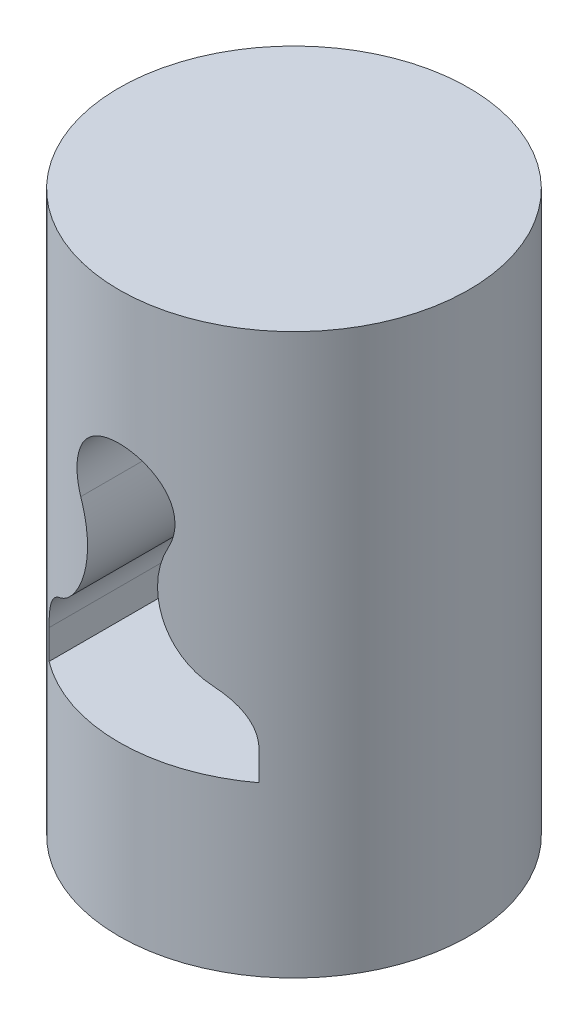
SolidWorks part; units mm, degrees
ref_plane "Front" through (0, 0, 0) normal (0, 0, 1) x (1, 0, 0)
ref_plane "Top" through (0, 0, 0) normal (0, 1, 0) x (1, 0, 0)
ref_plane "Right" through (0, 0, 0) normal (1, 0, 0) x (0, 0, -1)
sketch "Sketch2" plane through (0, 0, 0) normal (0, 1, 0) x (1, 0, 0)
  circle A0 centre (0, 0) radius 12.5
  dimension "D1" = 25
extrude "Boss-Extrude1" add sketch "Sketch2" along normal mid plane 40
sketch "Sketch3" plane through (0, 0, 0) normal (0, 0, 1) x (1, 0, 0)
  line L0 (-7.5, -8) -> (7.5, -8)
  line L1 (7.5, -8) -> (7.5, -5.9029)
  line L2 (-7.5, -5.9029) -> (-7.5, -8)
  arc A0 (7.5, -5.9029) -> (5.5, -2.4388) centre (3.5, -5.9029) ccw
  arc A1 (5.5, -2.4388) -> (3.1316, 5.4369) centre (8.5, 2.7574) cw
  arc A2 (3.1316, 5.4369) -> (-3.1316, 5.4369) centre (0, 7) ccw
  arc A3 (-3.1316, 5.4369) -> (-5.5, -2.4388) centre (-8.5, 2.7574) cw
  arc A4 (-5.5, -2.4388) -> (-7.5, -5.9029) centre (-3.5, -5.9029) ccw
  point P0 (0, -8)
  dimension "D1" = 3.5
  dimension "D6" = 6
  dimension "D7" = 17
  dimension "D2" = 15
  dimension "D3" = 7
  dimension "D4" = 15
  dimension "D5" = 8
extrude "Cut-Extrude1" cut sketch "Sketch3" against normal through all both and the other way through all
sketch "Sketch4" plane through (0, -20, 0) normal (0, -1, 0) x (-1, 0, 0)
  circle A0 centre (0, 0) radius 3
  dimension "D1" = 6
extrude "Cut-Extrude2" cut sketch "Sketch4" against normal blind 3
